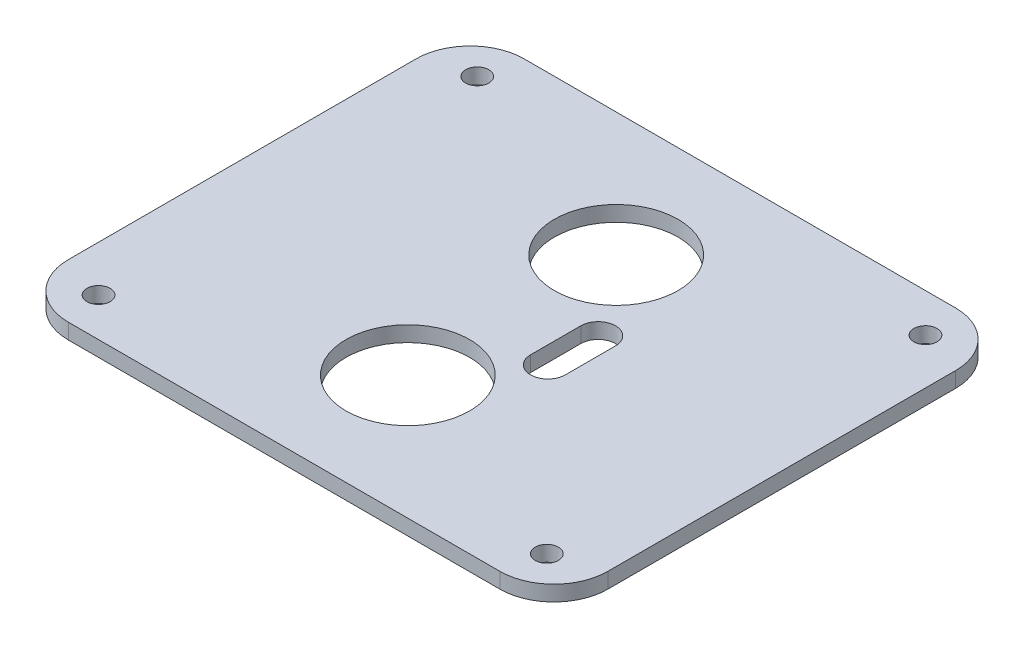
SolidWorks part; units mm, degrees
ref_plane "Front" through (0, 0, 0) normal (0, 0, 1) x (1, 0, 0)
ref_plane "Top" through (0, 0, 0) normal (0, 1, 0) x (1, 0, 0)
ref_plane "Right" through (0, 0, 0) normal (1, 0, 0) x (0, 0, -1)
sketch "草圖2" plane through (0, 0, 0) normal (0, 1, 0) x (-1, 0, 0)
  line L0 (-70.4577, 0) -> (70.2215, 0) construction
  line L1 (0, 52.2359) -> (0, -52.5789) construction
  line L2 (-34.9184, 29.5) -> (34.9184, -29.5) construction
  line L3 (-34.9184, -29.5) -> (34.9184, -29.5)
  line L4 (-34.9184, -29.5) -> (-34.9184, 29.5)
  line L5 (-34.9184, 29.5) -> (34.9184, 29.5)
  line L6 (34.9184, -29.5) -> (34.9184, 29.5)
  line L7 (0, 29.5) -> (0, -29.5) construction
  line L8 (-34.9184, 0) -> (34.9184, 0) construction
  line L9 (-7.9, 3.25) -> (-7.9, -3.25) construction
  line L10 (10.35, -22.25) -> (-10.35, -22.25) construction
  line L11 (10.35, -22.25) -> (10.35, 22.25) construction
  line L12 (10.35, 22.25) -> (-10.35, 22.25) construction
  line L13 (-10.35, -22.25) -> (-10.35, 22.25) construction
  line L14 (0, 22.25) -> (0, -22.25) construction
  line L15 (10.35, 0) -> (-10.35, 0) construction
  line L16 (-5.65, 3.25) -> (-5.65, -3.25)
  line L17 (-10.15, 3.25) -> (-10.15, -3.25)
  circle A0 centre (0, 13.48) radius 8
  circle A1 centre (0, -13.48) radius 8
  arc A2 (-5.65, 3.25) -> (-10.15, 3.25) centre (-7.9, 3.25) ccw
  circle A3 centre (29, 24.5) radius 1.5
  circle A4 centre (29, -24.5) radius 1.5
  circle A5 centre (-29, 24.5) radius 1.5
  circle A6 centre (-29, -24.5) radius 1.5
  arc A9 (-10.15, -3.25) -> (-5.65, -3.25) centre (-7.9, -3.25) ccw
  point P3 (0, 0)
  point P4 (0, 0)
  point P7 (0, 0)
  point P20 (0, 0)
  point P23 (0, 0)
  point P25 (0, 0)
  point P26 (0, 0)
  point P32 (-7.9, 0)
  dimension "D6" = 3
  dimension "D7" = 44.5
  dimension "D8" = 20.7
  dimension "D10" = 0.4
  dimension "D11" = 6.5
  dimension "D4" = 26.96
  dimension "D5" = 16
  dimension "D9" = 4.5
  dimension "D1" = 49
  dimension "D2" = 58
  dimension "D3" = 5
extrude "填料-伸長1" add sketch "草圖2" along normal blind 2
fillet "圓角1" radius 7 4 edges at (-34.9184, 1, 29.5) (-34.9184, 1, -29.5) (34.9184, 1, -29.5) (34.9184, 1, 29.5)
